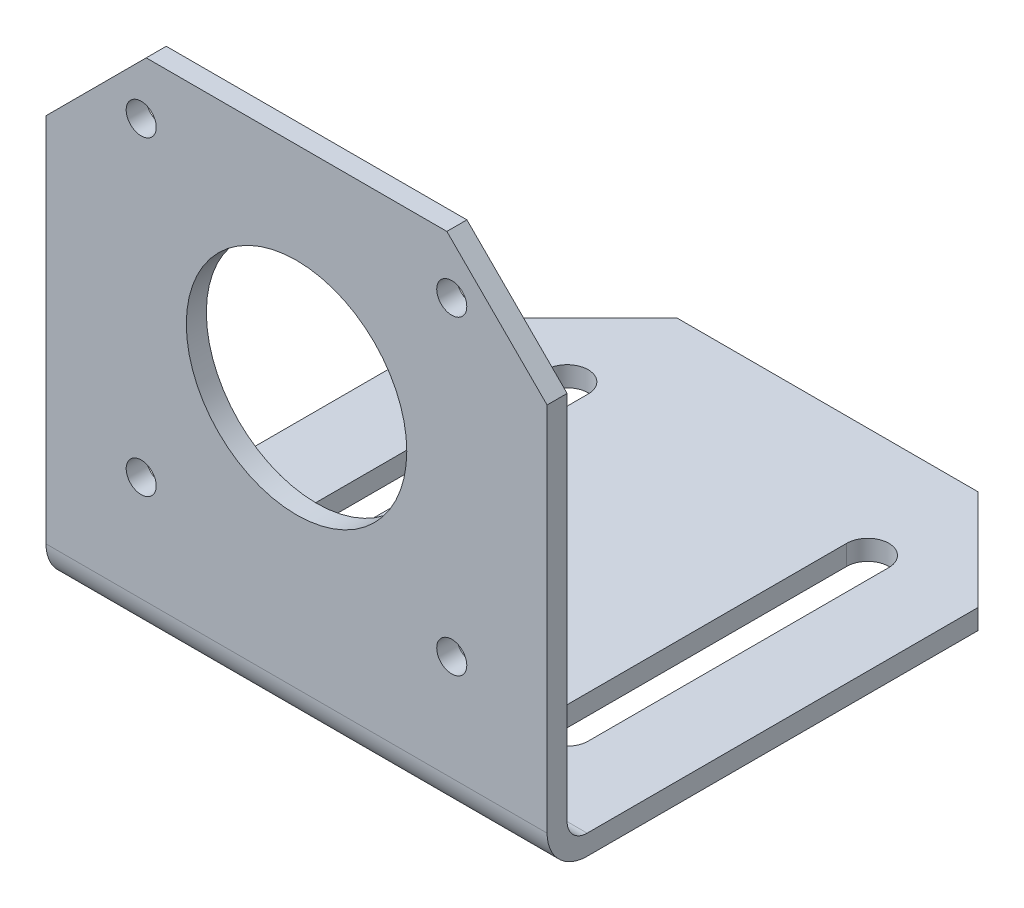
SolidWorks part; units mm, degrees
ref_plane "Front Plane" through (0, 0, 0) normal (0, 0, 1) x (1, 0, 0)
ref_plane "Top Plane" through (0, 0, 0) normal (0, 1, 0) x (1, 0, 0)
ref_plane "Right Plane" through (0, 0, 0) normal (1, 0, 0) x (0, 0, -1)
sketch "Sketch1" plane through (0, 0, 0) normal (1, 0, 0) x (0, 0, -1)
  line L0 (4, 0) -> (53, 0)
  line L1 (0, 4) -> (0, 51)
  line L2 (53, 0) -> (53, 2)
  line L3 (0, 51) -> (2, 51)
  line L4 (2, 51) -> (2, 4)
  line L5 (4, 2) -> (53, 2)
  arc A0 (2, 4) -> (4, 2) centre (4, 4) ccw
  arc A1 (4, 0) -> (0, 4) centre (4, 4) cw
  point P11 (0, 0)
  dimension "D1" = 2
  dimension "D2" = 4
extrude "Boss-Extrude1" add sketch "Sketch1" along normal blind 50 contours L1 L3 L4 A0 L5 L2 L0 A1
sketch "Sketch2" plane through (0, 0, -2) normal (0, 0, -1) x (-1, 0, 0)
  line L0 (-25, 51) -> (-25, 30) construction
  line L1 (-50, 51) -> (0, 51) construction
  line L2 (-25, 30) -> (-9.5, 30) construction
  line L3 (-9.5, 30) -> (-9.5, 45.5) construction
  circle A0 centre (-25, 30) radius 11
  circle A1 centre (-9.5, 45.5) radius 1.5
  circle A2 centre (-40.488, 45.5) radius 1.5
  circle A3 centre (-40.488, 14.5) radius 1.5
  circle A4 centre (-9.5, 14.5) radius 1.5
  dimension "D1" = 2
  dimension "D2" = 2
extrude "Cut-Extrude1" cut sketch "Sketch2" against normal up to surface (2 mm away) up to face at (25, 27.5, 0)
sketch "Sketch3" plane through (0, 2, 0) normal (0, 1, 0) x (1, 0, 0)
  line L0 (25, 53) -> (25, 4) construction
  line L1 (50, 53) -> (0, 53) construction
  line L2 (50, 4) -> (0, 4) construction
  line L3 (25, 53) -> (40, 53) construction
  line L4 (40, 53) -> (40, 42) construction
  line L5 (40, 42) -> (40, 12) construction
  line L6 (40, 42) -> (40, 12) construction
  line L7 (42.1, 42) -> (42.1, 12)
  line L8 (37.9, 42) -> (37.9, 12)
  line L9 (10, 42) -> (10, 12) construction
  line L10 (10, 42) -> (10, 12) construction
  line L11 (7.9, 42) -> (7.9, 12)
  line L12 (12.1, 42) -> (12.1, 12)
  arc A0 (42.1, 42) -> (37.9, 42) centre (40, 42) ccw
  arc A1 (37.9, 12) -> (42.1, 12) centre (40, 12) ccw
  arc A2 (7.9, 42) -> (12.1, 42) centre (10, 42) cw
  arc A3 (12.1, 12) -> (7.9, 12) centre (10, 12) cw
  point P6 (40, 27)
  point P16 (10, 27)
  dimension "D1" = 11
extrude "Cut-Extrude2" cut sketch "Sketch3" against normal up to surface (2 mm away) up to face at (25, 0, -28.5)
sketch "Sketch4" plane through (0, 2, 0) normal (0, 1, 0) x (1, 0, 0)
  line L0 (0, 43) -> (10, 53)
  line L5 (40, 53) -> (50, 43)
  line L6 (0, 43) -> (0, 53)
  line L7 (0, 53) -> (10, 53)
  line L8 (10, 53) -> (10.0546, 53.0315)
  line L9 (40, 53) -> (50, 53)
  line L10 (50, 53) -> (50, 43)
  point P0 (0, 53)
  point P3 (50, 53)
  line M9 (0, 53) -> (0, 4)
  line M11 (50, 4) -> (50, 53)
  line M12 (50, 53) -> (0, 53)
extrude "Cut-Extrude3" cut sketch "Sketch4" against normal up to surface (2 mm away) contours L0 M9 M12 | L5 M12 M11 up to face at (10, 0, -27)
sketch "Sketch5" plane through (0, 0, -2) normal (0, 0, -1) x (-1, 0, 0)
  line L0 (-50, 41) -> (-40, 51)
  line L5 (-10, 51) -> (0, 41)
  line L6 (-50, 41) -> (-50, 51)
  line L7 (-50, 51) -> (-40, 51)
  line L8 (-10, 51) -> (0, 51)
  line L9 (0, 51) -> (0, 41)
  point P0 (-50, 51)
  point P3 (0, 51)
extrude "Cut-Extrude4" cut sketch "Sketch5" against normal up to surface (2 mm away) up to face at (11, 45.5, 0)
